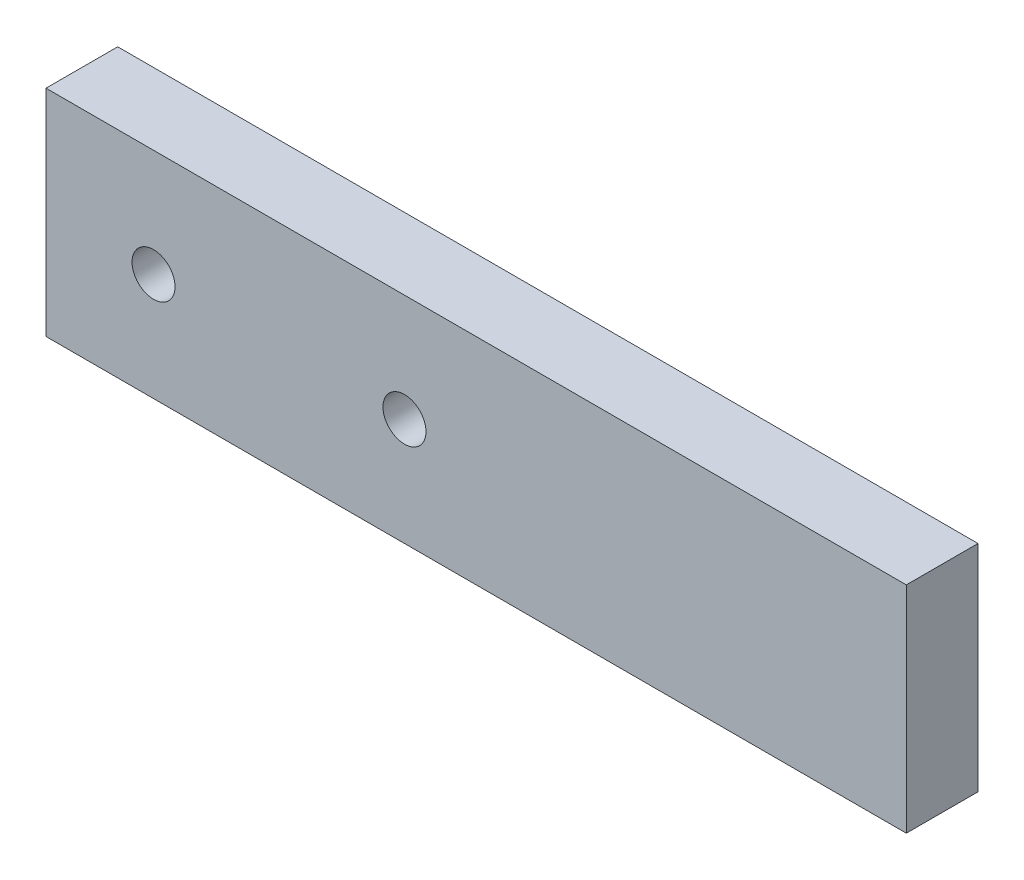
SolidWorks part; units mm, degrees
ref_plane "Front Plane" through (0, 0, 0) normal (0, 0, 1) x (1, 0, 0)
ref_plane "Top Plane" through (0, 0, 0) normal (0, 1, 0) x (1, 0, 0)
ref_plane "Right Plane" through (0, 0, 0) normal (1, 0, 0) x (0, 0, -1)
sketch "Sketch1" plane through (0, 0, 0) normal (0, 0, 1) x (1, 0, 0)
  line L1 (0, 0) -> (-60, 0)
  line L2 (0, 0) -> (0, 15)
  line L3 (0, 15) -> (-60, 15)
  line L4 (-60, 0) -> (-60, 15)
  circle A0 centre (-52.5, 7.5) radius 1.5
  circle A1 centre (-35, 7.5) radius 1.5
  dimension "D3" = 3
  dimension "D4" = 3
  dimension "D5" = 7.5
  dimension "D6" = 7.5
  dimension "D7" = 7.5
  dimension "D8" = 25
  dimension "D1" = 60
  dimension "D2" = 15
extrude "Boss-Extrude1" add sketch "Sketch1" along normal blind 5
